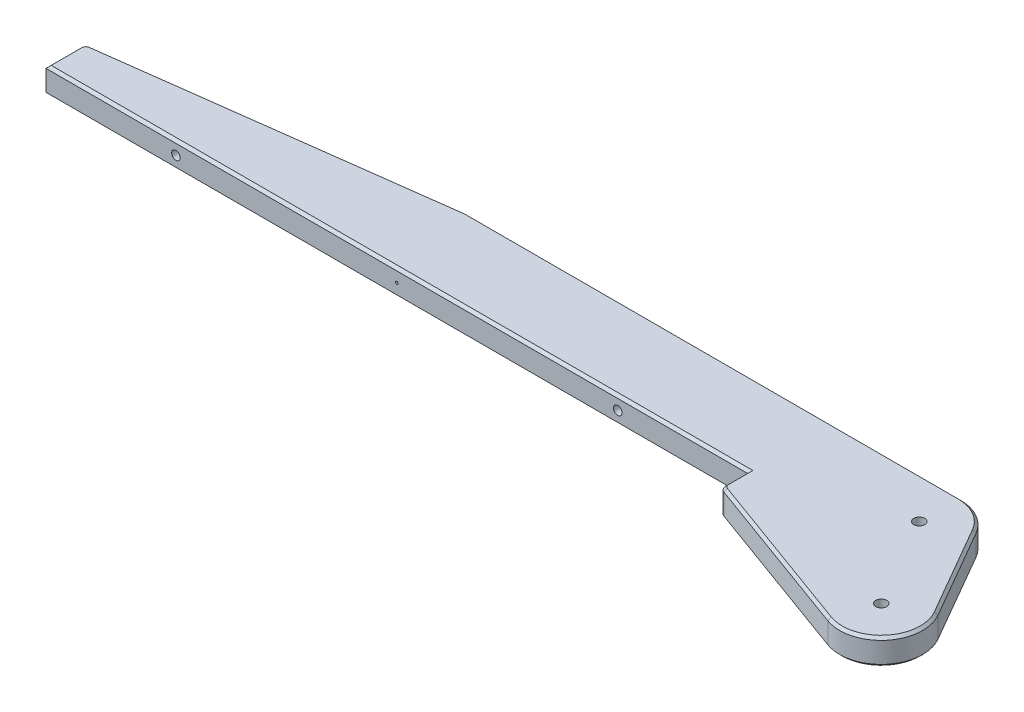
SolidWorks part; units mm, degrees
ref_plane "Front Plane" through (0, 0, 0) normal (0, 0, 1) x (1, 0, 0)
ref_plane "Top Plane" through (0, 0, 0) normal (0, 1, 0) x (1, 0, 0)
ref_plane "Right Plane" through (0, 0, 0) normal (1, 0, 0) x (0, 0, -1)
sketch "Sketch2" plane through (0, 0, 0) normal (0, 1, 0) x (1, 0, 0)
  line L0 (-210, 50.641) -> (-20, 50.641)
  line L1 (-6.1436, 42.641) -> (13.8564, 8)
  line L2 (-340, 33.641) -> (-340, 18.641)
  line L3 (-340, 18.641) -> (-70, 18.641)
  line L5 (-340, 33.641) -> (-210, 50.641)
  line L6 (-70, 18.641) -> (-70, 8.4511)
  line L7 (-5.4723, -15.0351) -> (-70, 8.4511)
  circle A1 centre (0, 0) radius 40 construction
  arc A2 (-6.1436, 42.641) -> (-20, 50.641) centre (-20, 34.641) ccw
  arc A3 (-5.4723, -15.0351) -> (13.8564, 8) centre (0, 0) ccw
  point P1 (-20, 34.641)
  dimension "D1" = 20
  dimension "D3" = 40
  dimension "D4" = 80
  dimension "D10" = 32
  dimension "D2" = 190
  dimension "D5" = 130
  dimension "D6" = 15
  dimension "D7" = 32
  dimension "D9" = 270
extrude "Boss-Extrude1" add sketch "Sketch2" along normal mid plane 10
hole_wizard "M5x0.8 Tapped Hole1" positions "Sketch3" profile "Sketch4" tap size "M5x0.8" standard "ANSI Metric" end condition through all
sketch "Sketch3" plane through (0, 5, 0) normal (0, 1, 0) x (1, 0, 0)
  point P0 (-20, 34.641)
  point P2 (0, 0)
sketch "Sketch4" plane through (-20, 5, -34.641) normal (1, 0, 0) x (0, 0, 1)
  line L0 (0, 0) -> (0, 10)
  line L1 (0, 10) -> (2.1, 10)
  line L2 (2.1, 10) -> (2.1, 0)
  line L5 (2.1, 0) -> (0, 0)
  line L11 (0, -6.35) -> (0, 107.95) construction
  dimension "Thru Tap Drill Dia." = 4.2
  dimension "Thru Tap Drill Depth" = 10
cosmetic thread "Hole Thread1" parameters "D2"=5
cosmetic thread "Hole Thread2" parameters "D2"=5
sketch "Sketch14" plane through (0, -5, 0) normal (0, -1, 0) x (1, 0, 0)
  circle A0 centre (0, 0) radius 4.15
  dimension "D1" = 8.3
extrude "Cut-Extrude2" cut sketch "Sketch14" against normal blind 6
hole_wizard "M4x0.7 Tapped Hole1" positions "Sketch12" profile "Sketch13" tap size "M4x0.7" standard "ANSI Metric"
sketch "Sketch12" plane through (0, 0, -18.641) normal (0, 0, 1) x (1, 0, 0)
  line L0 (36.6526, 0) -> (-36.6526, 0) construction
  line L1 (-340, 5) -> (-340, -5) construction
  line L2 (-70, 5) -> (-70, -5) construction
  point P0 (-290, 0)
  point P2 (-120, 0)
  dimension "D1" = 50
  dimension "D2" = 50
sketch "Sketch13" plane through (-290, 0, -18.641) normal (1, 0, 0) x (0, -1, 0)
  line L0 (0, 0) -> (0, 15.9914)
  line L1 (0, 15.9914) -> (1.65, 15)
  line L2 (1.65, 15) -> (1.65, 0)
  line L5 (1.65, 0) -> (0, 0)
  line L10 (0, 15.9914) -> (-1.65, 15) construction
  line L11 (0, -6.35) -> (0, 107.95) construction
  dimension "Tap Drill Dia." = 3.3
  dimension "Tap Drill Depth" = 15
  dimension "Drill Angle" = 118
cosmetic thread "Hole Thread3" parameters "D1"=14.3, "D2"=4
cosmetic thread "Hole Thread4" parameters "D1"=14.3, "D2"=4
fillet "Fillet1" radius 2.5 3 edges at (-70, 0, -8.4511) (-210, 0, -50.641) (-340, 0, -33.641)
chamfer "Chamfer1" distance 1 angle 45 24 edges at (-70, -5, -14.4213) (-69.5479, -5, -8.7676) (-36.9137, -5, 3.5914) (12.2567, -5, 10.2846) (3.8564, -5, -25.3205) (-12, -5, -48.4974) (-114.9186, -5, -50.641) (-209.9997, -5, -50.6357) (-273.9928, -5, -42.2727) (-339.3789, -5, -33.0958) (-340, -5, -25.0438) (-205, -5, -18.641) (-209.9997, 5, -50.6357) (-114.9186, 5, -50.641) (-12, 5, -48.4974) (3.8564, 5, -25.3205) (12.2567, 5, 10.2846) (-36.9137, 5, 3.5914) (-69.5479, 5, -8.7676) (-70, 5, -14.4213) (-205, 5, -18.641) (-340, 5, -25.0438) (-339.3789, 5, -33.0958) (-273.9928, 5, -42.2727)
hole_wizard "Ø1.0mm Dowel Hole1" positions "Sketch15" profile "Sketch16" hole size "Ø1.0" standard "ANSI Metric"
sketch "Sketch15" plane through (0, 0, -18.641) normal (0, 0, 1) x (1, 0, 0)
  line L0 (36.6526, 0) -> (-36.6526, 0) construction
  circle A0 centre (-290, 0) radius 1.65 construction
  point P0 (-205, 0)
  dimension "D1" = 85
sketch "Sketch16" plane through (-205, 0, -18.641) normal (1, 0, 0) x (0, -1, 0)
  line L0 (0, 0) -> (0, 5.3004)
  line L1 (0, 5.3004) -> (0.5, 5)
  line L2 (0.5, 5) -> (0.5, 0)
  line L5 (0.5, 0) -> (0, 0)
  line L10 (0, 5.3004) -> (-0.5, 5) construction
  line L11 (0, -6.35) -> (0, 107.95) construction
  dimension "Hole Dia." = 1
  dimension "Hole Depth" = 5
  dimension "Drill Angle" = 118
